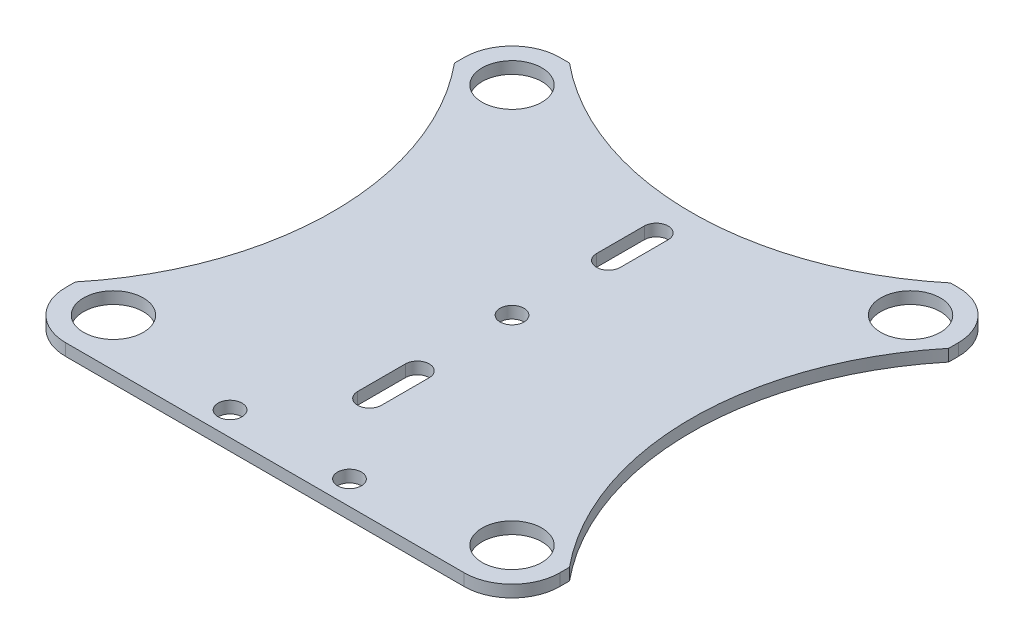
SolidWorks part; units mm, degrees
ref_plane "Front Plane" through (0, 0, 0) normal (0, 0, 1) x (1, 0, 0)
ref_plane "Top Plane" through (0, 0, 0) normal (0, 1, 0) x (1, 0, 0)
ref_plane "Right Plane" through (0, 0, 0) normal (1, 0, 0) x (0, 0, -1)
sketch "Sketch1" plane through (0, 0, 0) normal (0, 1, 0) x (1, 0, 0)
  line L0 (32.0389, 41.3689) -> (33.3689, 41.3689)
  line L1 (-33.3689, -41.3689) -> (-31.7434, -41.3689)
  line L2 (-41.3689, -33.3689) -> (-41.3689, -31.7434)
  line L3 (-33.3689, 41.3689) -> (-31.7434, 41.3689)
  line L4 (41.3689, -33.3689) -> (41.3689, -31.7434)
  line L5 (-41.3689, -41.3689) -> (41.3689, 41.3689) construction
  line L6 (-41.3689, 41.3689) -> (41.3689, -41.3689) construction
  line L7 (41.3689, 31.7434) -> (41.3689, 33.3689)
  line L8 (32.0389, -41.3689) -> (33.3689, -41.3689)
  line L9 (-41.3689, 31.7434) -> (-41.3689, 33.3689)
  line L10 (0.1478, 29.906) -> (0.1478, -29.906) construction
  line L11 (0.1478, 24) -> (0.1478, 16) construction
  line L12 (2.1478, 24) -> (2.1478, 16)
  line L13 (-1.8522, 24) -> (-1.8522, 16)
  line L14 (-30, 0) -> (30, 0) construction
  line L15 (0.1478, -24) -> (0.1478, -16) construction
  line L16 (-1.8522, -24) -> (-1.8522, -16)
  line L17 (2.1478, -24) -> (2.1478, -16)
  line L18 (-31.7434, -41.3689) -> (32.0389, -41.3689)
  arc A0 (-31.7434, 41.3689) -> (32.0389, 41.3689) centre (0.1478, 79.9999) ccw
  arc A1 (41.3689, 31.7434) -> (41.3689, -31.7434) centre (80, 0) ccw
  arc A3 (-41.3689, -31.7434) -> (-41.3689, 31.7434) centre (-80, 0) ccw
  arc A4 (-41.3689, -33.3689) -> (-33.3689, -41.3689) centre (-33.3689, -33.3689) ccw
  arc A5 (33.3689, -41.3689) -> (41.3689, -33.3689) centre (33.3689, -33.3689) ccw
  arc A6 (33.3689, 41.3689) -> (41.3689, 33.3689) centre (33.3689, 33.3689) cw
  arc A7 (-41.3689, 33.3689) -> (-33.3689, 41.3689) centre (-33.3689, 33.3689) cw
  arc A8 (2.1478, 24) -> (-1.8522, 24) centre (0.1478, 24) ccw
  arc A9 (-1.8522, 16) -> (2.1478, 16) centre (0.1478, 16) ccw
  arc A10 (-1.8522, -24) -> (2.1478, -24) centre (0.1478, -24) ccw
  arc A11 (2.1478, -16) -> (-1.8522, -16) centre (0.1478, -16) ccw
  circle A12 centre (-33.3689, 33.3689) radius 5
  circle A13 centre (33.3689, 33.3689) radius 5
  circle A14 centre (-33.3689, -33.3689) radius 5
  circle A15 centre (33.3689, -33.3689) radius 5
  circle A16 centre (0, 0) radius 2
  circle A17 centre (10.1478, -37.3613) radius 2
  circle A18 centre (-9.8522, -37.3613) radius 2
  point P0 (0, 0)
  point P16 (0.1478, 20)
  point P43 (0.1478, -20)
  dimension "D2" = 80
  dimension "D3" = 80
  dimension "D4" = 10
  dimension "D5" = 8
  dimension "D6" = 40
  dimension "D1" = 80
  dimension "D7" = 20
extrude "Boss-Extrude1" add sketch "Sketch1" along normal blind 2
